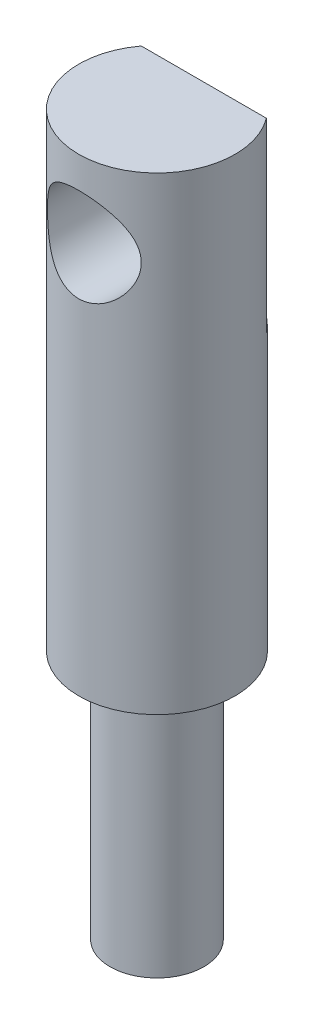
SolidWorks part; units mm, degrees
material "非常高密度 PE (SS)"
ref_plane "前视基准面" through (0, 0, 0) normal (0, 0, 1) x (1, 0, 0)
ref_plane "上视基准面" through (0, 0, 0) normal (0, 1, 0) x (1, 0, 0)
ref_plane "右视基准面" through (0, 0, 0) normal (1, 0, 0) x (0, 0, -1)
sketch "草图1" plane through (0, 0, 0) normal (0, 0, 1) x (1, 0, 0)
  line L0 (0, 9.186) -> (0, -9.7231) construction
  line L1 (0, 0) -> (2.5, 0)
  line L2 (2.5, 0) -> (2.5, -15)
  line L3 (2.5, -15) -> (1.5, -15)
  line L4 (1.5, -15) -> (1.5, -23)
  line L5 (1.5, -23) -> (0, -23)
  line L6 (0, -23) -> (0, 0)
  dimension "D1" = 2.5
  dimension "D2" = 15
  dimension "D3" = 1.5
  dimension "D4" = 8
revolve "旋转1" add sketch "草图1" angle 360 about L0
cosmetic thread "装饰螺纹线1" parameters "D2"=2
sketch "草图2" plane through (0, 0, 0) normal (0, 1, 0) x (1, 0, 0)
  line L0 (-2.5, 0) -> (2.5, 0) construction
  line L1 (-2, 1.5) -> (2, 1.5)
  circle A0 centre (0, 0) radius 2.5 construction
  arc A1 (2, 1.5) -> (-2, 1.5) centre (0, 0) ccw
  dimension "D1" = 1.5
extrude "切除-拉伸1" cut sketch "草图2" against normal blind 6
sketch "草图3" plane through (0, 0, -1.5) normal (0, 0, -1) x (-1, 0, 0)
  line L0 (2, 0) -> (-2, 0) construction
  line L1 (0, 0) -> (0, -6) construction
  line L2 (2, -6) -> (-2, -6) construction
  circle A0 centre (0, -2.5) radius 1.5
  dimension "D1" = 3
  dimension "D2" = 2.5
extrude "切除-拉伸2" cut sketch "草图3" against normal through all
